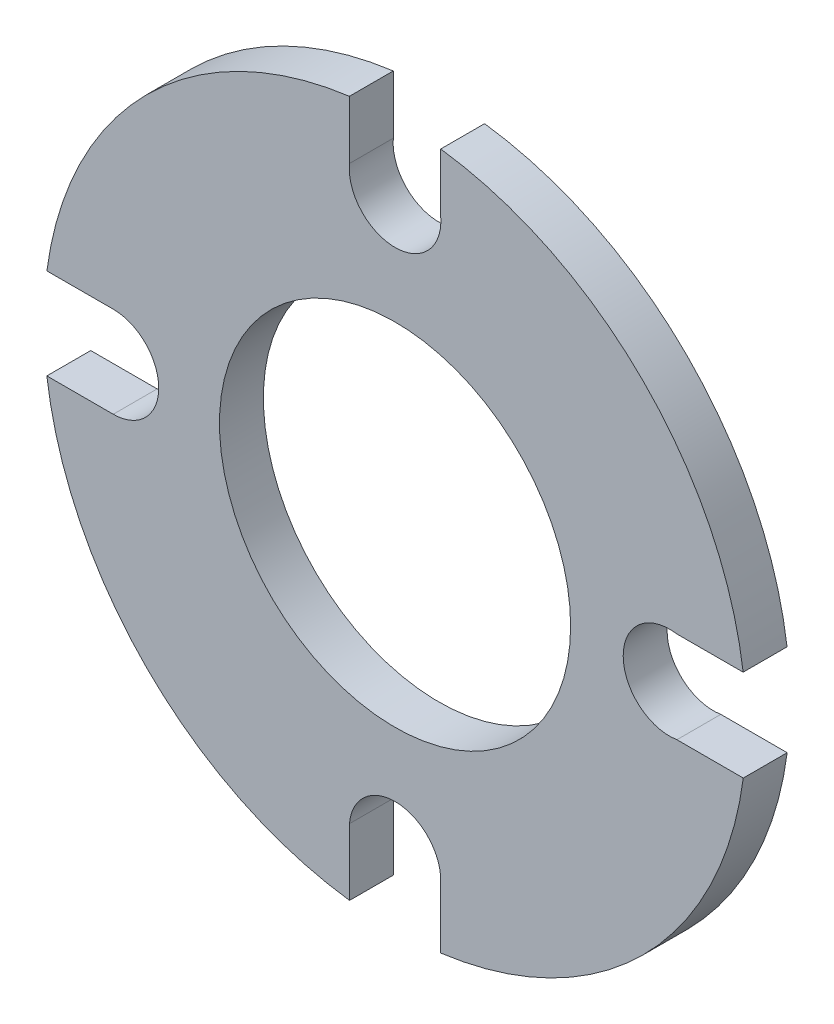
SolidWorks part; units mm, degrees
material "AISI 1045 Steel, cold drawn"
ref_plane "Front Plane" through (0, 0, 0) normal (0, 0, 1) x (1, 0, 0)
ref_plane "Top Plane" through (0, 0, 0) normal (0, 1, 0) x (1, 0, 0)
ref_plane "Right Plane" through (0, 0, 0) normal (1, 0, 0) x (0, 0, -1)
sketch "Sketch1" plane through (0, 0, 0) normal (0, 0, 1) x (1, 0, 0)
  line L1 (80.227, 13.1648) -> (99.1273, 13.1821)
  line L2 (-13, 100) -> (-13, 99.1514)
  line L3 (-99.1657, -12.8902) -> (-80.2527, -12.8914)
  line L4 (-13, 80.2539) -> (-13, 99.1514)
  line L5 (-99.1514, 13) -> (-80.2511, 13.0173)
  line L6 (13, 99.1514) -> (12.9985, 80.2542)
  line L7 (-12.9843, -80.2378) -> (-12.9649, -99.156)
  line L10 (80.2698, -12.9015) -> (99.1641, -12.9027)
  line L14 (12.9858, -80.2562) -> (12.9843, -99.1535)
  arc A0 (99.1273, 13.1821) -> (13, 99.1514) centre (0, 0) ccw
  circle A1 centre (0, 0) radius 50
  arc A4 (12.9858, -80.2562) -> (-12.9843, -80.2378) centre (0, -81.3) ccw
  arc A5 (80.227, 13.1648) -> (80.2698, -12.9015) centre (78.167, 0.1282) ccw
  arc A6 (-80.2527, -12.8914) -> (-80.2511, 13.0173) centre (-80.2519, 0.063) ccw
  arc A7 (-13, 82.5693) -> (12.9987, 82.5839) centre (0, 81.4116) ccw
  arc A8 (-13, 99.1514) -> (-99.1514, 13) centre (0, 0) ccw
  arc A11 (12.9843, -99.1535) -> (99.1641, -12.9027) centre (0, 0) ccw
  arc A13 (-99.1657, -12.8902) -> (-12.9649, -99.156) centre (0, 0) ccw
  dimension "D1" = 200
  dimension "D2" = 100
extrude "Boss-Extrude1" add sketch "Sketch1" along normal blind 12.5 contours L3 A13 L7 A4 L14 A11 L10 A5 L1 A0 L6 A7 L4 A8 L5 A6 A1
